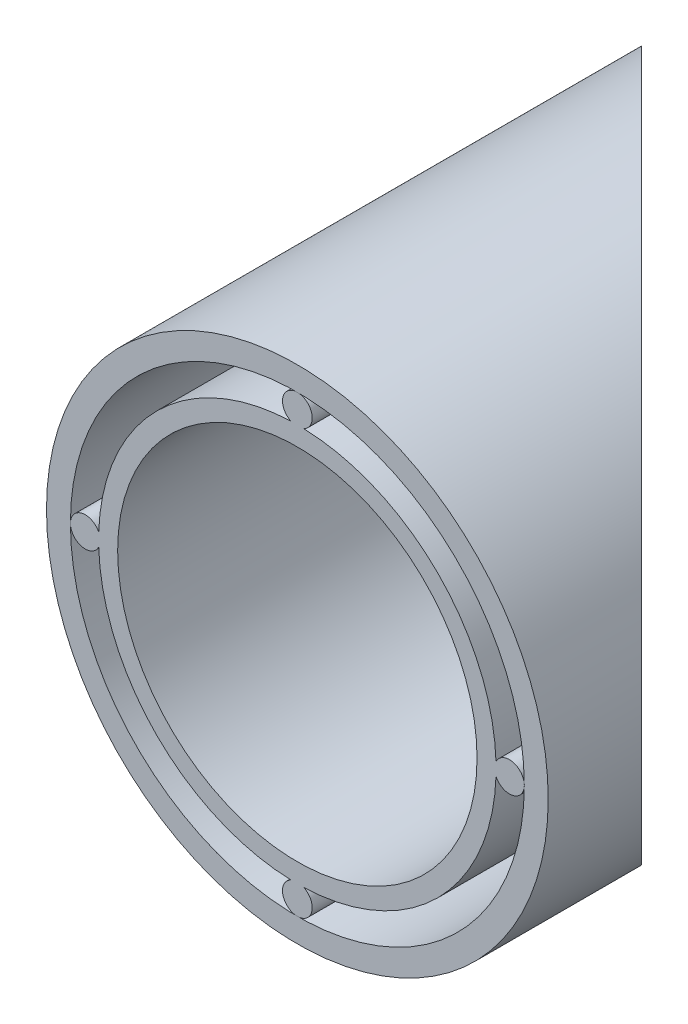
SolidWorks part; units mm, degrees
ref_plane "Front Plane" through (0, 0, 0) normal (0, 0, 1) x (1, 0, 0)
ref_plane "Top Plane" through (0, 0, 0) normal (0, 1, 0) x (1, 0, 0)
ref_plane "Right Plane" through (0, 0, 0) normal (1, 0, 0) x (0, 0, -1)
sketch "Sketch1" plane through (0, 0, 0) normal (0, 0, 1) x (1, 0, 0)
  circle A0 centre (0, 0) radius 21.08
  circle A1 centre (0, 0) radius 19.07
  dimension "D1" = 42.16
  dimension "D2" = 2.01
  dimension "D3" = 38.14
extrude "Boss-Extrude1" add sketch "Sketch1" against normal blind 50
sketch "Sketch2" plane through (0, 0, 0) normal (0, 1, 0) x (1, 0, 0)
  line L0 (-21.08, 50) -> (21.08, 7.84)
  line L1 (21.08, 0) -> (21.08, 50) construction
  line L2 (19.07, 50) -> (-19.07, 50) construction
  line L3 (21.08, 50) -> (-21.08, 50) construction
  line L4 (21.08, 7.84) -> (21.08, 50)
  line L5 (21.08, 50) -> (-21.08, 50)
  dimension "D1" = 45
sketch "Sketch3" plane through (0, 0, 0) normal (0, 0, 1) x (1, 0, 0)
  circle A0 centre (0, 0) radius 16.7
  circle A1 centre (0, 0) radius 15.1
  dimension "D1" = 33.4
  dimension "D2" = 1.6
extrude "Boss-Extrude2" add sketch "Sketch3" against normal blind 50 separate body
sketch "Sketch4" plane through (0, 0, 0) normal (0, 0, 1) x (1, 0, 0)
  circle A0 centre (0, -17.82) radius 1.25
  circle A6 centre (-17.82, 0) radius 1.25
  circle A7 centre (0, 17.82) radius 1.25
  circle A8 centre (17.82, 0) radius 1.25
  point P12 (0, 0)
  dimension "D1" = 4
  dimension "D4" = 2.5
  dimension "D5" = 17.82
extrude "Boss-Extrude3" add sketch "Sketch4" against normal blind 50
extrude "Cut-Extrude1" cut sketch "Sketch2" against normal mid plane 153
